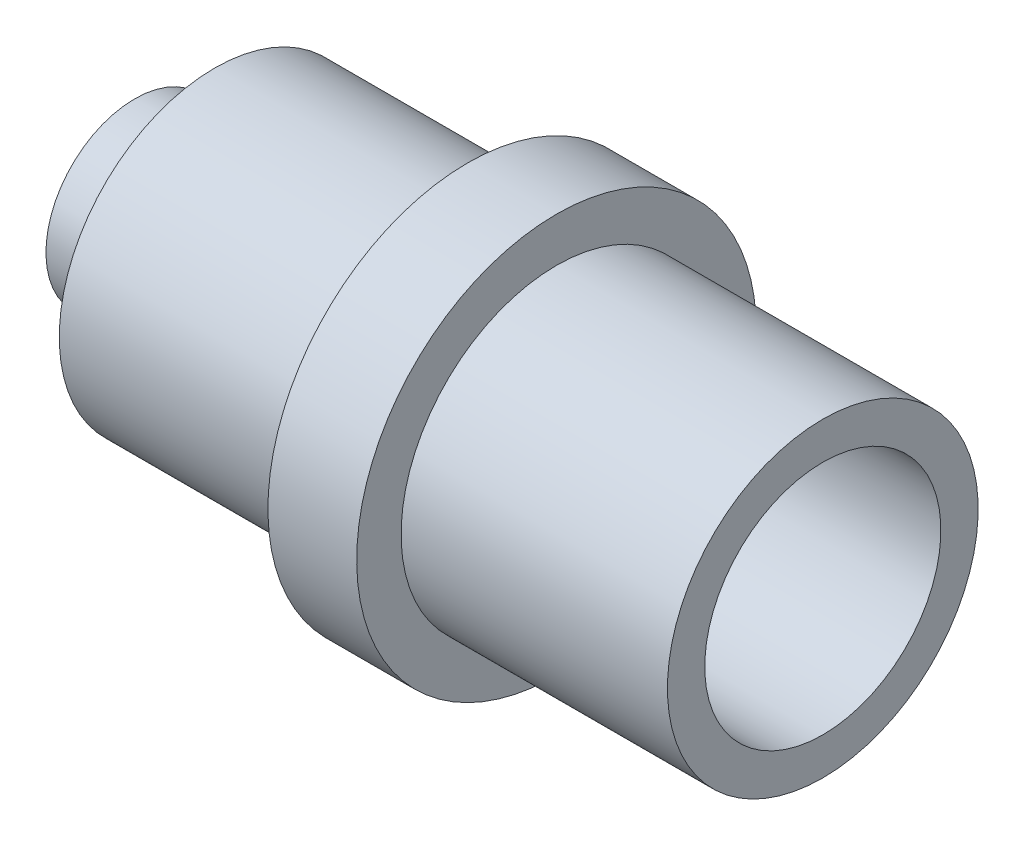
SolidWorks part; units mm, degrees
ref_plane "Front Plane" through (0, 0, 0) normal (0, 0, 1) x (1, 0, 0)
ref_plane "Top Plane" through (0, 0, 0) normal (0, 1, 0) x (1, 0, 0)
ref_plane "Right Plane" through (0, 0, 0) normal (1, 0, 0) x (0, 0, -1)
sketch "Sketch1" plane through (0, 0, 0) normal (0, 0, 1) x (1, 0, 0)
  line L0 (0, 0) -> (0, -3.5)
  line L1 (0, -3.5) -> (-6, -3.5)
  line L2 (-6, -3.5) -> (-6, -4.5)
  line L3 (-6, -4.5) -> (-8, -4.5)
  line L4 (-8, -4.5) -> (-8, -3.5)
  line L5 (-8, -3.5) -> (-13.7, -3.5)
  line L6 (-13.7, -3.5) -> (-13.7, -2)
  line L7 (-13.7, -2) -> (-15.5, -2)
  line L8 (0, 0) -> (-15.5, 0)
  line L9 (-15.5, -2) -> (-15.5, 0)
  point P13 (-13.7, -2.75)
  dimension "D1" = 6
  dimension "D2" = 3.5
  dimension "D3" = 4.5
  dimension "D4" = 13.7
  dimension "D5" = 3.5
  dimension "D6" = 15.5
  dimension "D7" = 2
  dimension "D8" = 2
revolve "Revolve1" add sketch "Sketch1" angle 360 about L8
sketch "Sketch2" plane through (0, 0, 0) normal (1, 0, 0) x (0, 0, -1)
  circle A0 centre (0, 0) radius 2.6597
extrude "Cut-Extrude1" cut sketch "Sketch2" against normal blind 5
